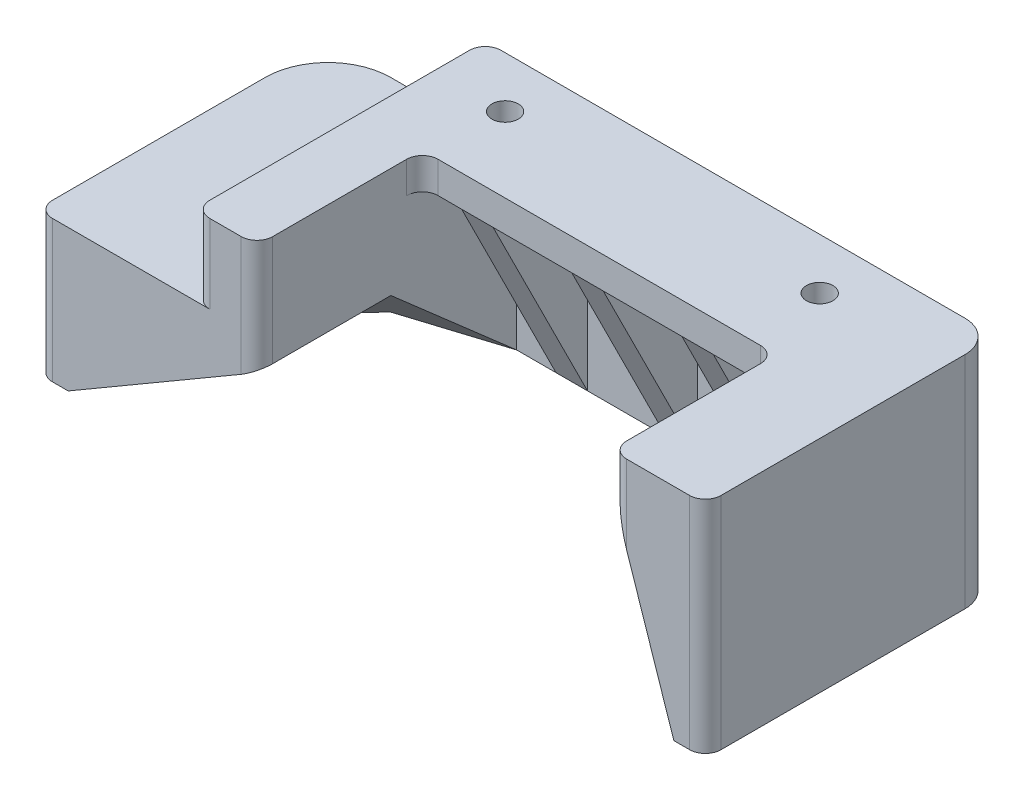
SolidWorks part; units mm, degrees
ref_plane "Front Plane" through (0, 0, 0) normal (0, 0, 1) x (1, 0, 0)
ref_plane "Top Plane" through (0, 0, 0) normal (0, 1, 0) x (1, 0, 0)
ref_plane "Right Plane" through (0, 0, 0) normal (1, 0, 0) x (0, 0, -1)
sketch "Sketch1" plane through (0, 0, 0) normal (0, 1, 0) x (-1, 0, 0)
  line L0 (0, 0) -> (141.2875, 0)
  line L2 (141.2875, 0) -> (141.2875, 65.1236)
  line L5 (0, 65.1236) -> (0, 0)
  line L6 (141.2875, 65.1236) -> (0, 65.1236)
  circle A0 centre (6.35, 16.6371) radius 2.667
  circle A9 centre (6.35, 42.0371) radius 2.667
  circle A10 centre (6.35, 67.4371) radius 2.667
  circle A11 centre (19.05, 16.6371) radius 2.667
  circle A12 centre (31.75, 16.6371) radius 2.667
  circle A13 centre (44.45, 16.6371) radius 2.667
  circle A14 centre (57.15, 16.6371) radius 2.667
  circle A15 centre (69.85, 16.6371) radius 2.667
  circle A16 centre (82.55, 16.6371) radius 2.667
  circle A17 centre (95.25, 16.6371) radius 2.667
  circle A18 centre (107.95, 16.6371) radius 2.667
  point P2 (0, 0)
  point P6 (0, 0)
  point P22 (0, 0)
  point P23 (0, 0)
  point P24 (0, 0)
  point P25 (-349.7027, -333.8065)
  point P28 (0, 0)
  point P29 (0, 0)
  point P30 (0, 0)
  point P31 (6.35, 42.0371)
  dimension "D1" = 5.334
  dimension "D4" = 25.4
  dimension "D5" = 25.4
  dimension "D6" = 9
  dimension "D7" = 12.7
  dimension "D2" = 65.1236
  dimension "D3" = 141.2875
  dimension "D8" = 6.35
  dimension "D9" = 16.6371
sketch "Sketch2" plane through (0, 0, 0) normal (0, 1, 0) x (1, 0, 0)
  line L0 (-141.2875, 0) -> (-141.2875, -65.1236) construction
  line L19 (-109.5375, -9.525) -> (-109.5375, -61.9486)
  line L20 (-6.35, -6.35) -> (-141.2875, -6.35)
  line L21 (-6.35, -65.1236) -> (-6.35, -6.35)
  line L22 (-12.7, -6.35) -> (-106.3625, -6.35)
  line L23 (-6.35, -61.9486) -> (-6.35, -12.7)
  line L27 (-106.3625, -65.1236) -> (-100.0125, -65.1236)
  line L28 (-141.2875, -65.1236) -> (0, -65.1236) construction
  line L29 (-96.8375, -61.9486) -> (-96.8375, -34.925)
  line L30 (-93.6625, -31.75) -> (-28.575, -31.75)
  line L31 (-25.4, -34.925) -> (-25.4, -61.9486)
  line L32 (-22.225, -65.1236) -> (-9.525, -65.1236)
  arc A4 (-6.35, -12.7) -> (-12.7, -6.35) centre (-12.7, -12.7) ccw
  circle A6 centre (-95.25, -16.6371) radius 2.667
  circle A7 centre (-31.75, -16.6371) radius 2.667
  arc A8 (-109.5375, -9.525) -> (-106.3625, -6.35) centre (-106.3625, -9.525) cw
  arc A12 (-100.0125, -65.1236) -> (-96.8375, -61.9486) centre (-100.0125, -61.9486) ccw
  arc A13 (-25.4, -61.9486) -> (-22.225, -65.1236) centre (-22.225, -61.9486) ccw
  arc A14 (-6.35, -61.9486) -> (-9.525, -65.1236) centre (-9.525, -61.9486) cw
  arc A15 (-28.575, -31.75) -> (-25.4, -34.925) centre (-28.575, -34.925) cw
  arc A16 (-96.8375, -34.925) -> (-93.6625, -31.75) centre (-93.6625, -34.925) cw
  arc A17 (-106.3625, -65.1236) -> (-109.5375, -61.9486) centre (-106.3625, -61.9486) cw
  point P3 (-115.8875, -65.1236)
  point P9 (0, 0)
  point P11 (-115.8875, -66.1497)
  point P23 (0, 0)
  point P26 (0, 0)
  point P30 (-109.5375, -6.35)
  point P31 (-109.5375, -65.1236)
  point P33 (-112.7125, -50.6865)
  point P34 (0, 0)
  point P42 (-96.8375, -65.1236)
  point P45 (-25.4, -65.1236)
  dimension "D1" = 6.35
  dimension "D2" = 6.35
  dimension "D3" = 19.05
  dimension "D7" = 25.4
  dimension "D4" = 5.334
  dimension "D9" = 3.175
  dimension "D10" = 3.175
  dimension "D5" = 31.75
  dimension "D8" = 12.7
extrude "Boss-Extrude1" add sketch "Sketch2" against normal blind 6.35
sketch "Sketch3" plane through (0, -6.35, 0) normal (0, -1, 0) x (1, 0, 0)
  line L0 (-6.35, 61.9486) -> (-6.35, 12.7) construction
  line L1 (-12.7, 6.35) -> (-106.3625, 6.35) construction
  line L2 (-6.35, 61.9486) -> (-6.35, 12.7)
  line L3 (-12.7, 6.35) -> (-96.8375, 6.35)
  line L4 (-96.8375, 6.35) -> (-96.8375, 12.7)
  line L5 (-12.7, 58.7736) -> (-12.7, 49.2486)
  line L6 (-15.875, 12.7) -> (-38.1, 12.7)
  line L7 (-12.7, 58.7736) -> (-12.7, 12.7) construction
  line L8 (-12.7, 12.7) -> (-96.8375, 12.7) construction
  line L9 (-6.35, 58.7736) -> (-6.35, 12.7) construction
  line L10 (-141.2875, 65.1236) -> (0, 65.1236) construction
  line L11 (-9.525, 65.1236) -> (-22.225, 65.1236)
  line L12 (-25.4, 61.9486) -> (-25.4, 58.7736)
  line L13 (-25.4, 34.925) -> (-25.4, 61.9486) construction
  line L14 (-25.4, 58.7736) -> (-12.7, 58.7736)
  line L15 (-12.7, 42.8986) -> (-25.4, 42.8986)
  line L16 (-25.4, 42.8986) -> (-25.4, 49.2486)
  line L17 (-25.4, 49.2486) -> (-12.7, 49.2486)
  line L18 (-12.7, 27.0236) -> (-25.4, 27.0236)
  line L19 (-25.4, 27.0236) -> (-25.4, 33.3736)
  line L20 (-25.4, 33.3736) -> (-12.7, 33.3736)
  line L21 (-12.7, 27.0236) -> (-12.7, 15.875)
  line L22 (-12.7, 42.8986) -> (-12.7, 33.3736)
  line L23 (-38.1, 12.7) -> (-38.1, 31.75)
  line L24 (-38.1, 31.75) -> (-44.45, 31.75)
  line L25 (-93.6625, 31.75) -> (-28.575, 31.75) construction
  line L26 (-44.45, 31.75) -> (-44.45, 12.7)
  line L27 (-44.45, 12.7) -> (-60.325, 12.7)
  line L28 (-60.325, 12.7) -> (-60.325, 31.75)
  line L29 (-60.325, 31.75) -> (-66.675, 31.75)
  line L30 (-66.675, 31.75) -> (-66.675, 12.7)
  line L31 (-88.9, 12.7) -> (-96.8375, 12.7)
  line L33 (-82.55, 12.7) -> (-82.55, 31.75)
  line L34 (-82.55, 31.75) -> (-88.9, 31.75)
  line L35 (-88.9, 12.7) -> (-88.9, 31.75)
  line L36 (-66.675, 12.7) -> (-82.55, 12.7)
  arc A0 (-12.7, 6.35) -> (-6.35, 12.7) centre (-12.7, 12.7) ccw construction
  arc A1 (-12.7, 6.35) -> (-6.35, 12.7) centre (-12.7, 12.7) ccw
  arc A2 (-22.225, 65.1236) -> (-25.4, 61.9486) centre (-22.225, 61.9486) ccw
  arc A4 (-6.35, 61.9486) -> (-9.525, 65.1236) centre (-9.525, 61.9486) ccw
  arc A5 (-12.7, 15.875) -> (-15.875, 12.7) centre (-15.875, 15.875) cw
  arc A6 (-12.7, 12.7) -> (-12.7, 12.7) centre (-12.7, 12.7) ccw construction
  point P33 (-25.4, 65.1236)
  point P36 (-6.35, 65.1236)
  dimension "D2" = 3.175
  dimension "D8" = 3.175
  dimension "D1" = 6.35
  dimension "D3" = 6.35
  dimension "D4" = 6.35
  dimension "D5" = 9.525
  dimension "D6" = 6.35
  dimension "D7" = 9.525
  dimension "D9" = 6.35
  dimension "D10" = 6.35
  dimension "D11" = 6.35
  dimension "D12" = 6.35
  dimension "D13" = 15.875
  dimension "D14" = 15.875
extrude "Boss-Extrude2" add sketch "Sketch3" along normal blind 38.1
sketch "Sketch4" plane through (-88.9, 0, 0) normal (-1, 0, 0) x (0, 0, 1)
  line L0 (31.75, -6.35) -> (12.7, -44.45)
  line L1 (31.75, -44.45) -> (12.7, -44.45) construction
  line L2 (12.7, -44.45) -> (12.7, -6.35) construction
  line L3 (12.7, -44.45) -> (31.75, -44.45)
  line L4 (31.75, -44.45) -> (31.75, -6.35)
extrude "Cut-Extrude1" cut sketch "Sketch4" against normal up to surface (50.8 mm away) up to face at (-38.1, -25.4, 22.225)
sketch "Sketch5" plane through (0, 0, 65.1236) normal (0, 0, 1) x (1, 0, 0)
  line L0 (-25.4, -6.35) -> (-12.7, -44.45)
  line L1 (-9.525, -44.45) -> (-22.225, -44.45) construction
  line L2 (-12.7, -44.45) -> (-25.4, -44.45)
  line L3 (-25.4, -44.45) -> (-25.4, -6.35)
  point P5 (0, 0)
extrude "Cut-Extrude2" cut sketch "Sketch5" against normal up to surface (38.1 mm away) up to face at (-19.05, -25.4, 27.0236)
sketch "Sketch6" plane through (0, -6.35, 0) normal (0, -1, 0) x (1, 0, 0)
  line L0 (-96.8375, 6.35) -> (-106.3625, 6.35) construction
  line L1 (-109.5375, 9.525) -> (-109.5375, 61.9486) construction
  line L2 (-96.8375, 6.35) -> (-106.3625, 6.35)
  line L3 (-109.5375, 9.525) -> (-109.5375, 61.9486)
  line L4 (-106.3625, 65.1236) -> (-100.0125, 65.1236)
  line L5 (-96.8375, 61.9486) -> (-96.8375, 6.35)
  arc A0 (-109.5375, 9.525) -> (-106.3625, 6.35) centre (-106.3625, 9.525) ccw construction
  arc A1 (-106.3625, 65.1236) -> (-109.5375, 61.9486) centre (-106.3625, 61.9486) ccw construction
  arc A2 (-96.8375, 61.9486) -> (-100.0125, 65.1236) centre (-100.0125, 61.9486) ccw construction
  arc A3 (-109.5375, 9.525) -> (-106.3625, 6.35) centre (-106.3625, 9.525) ccw
  arc A4 (-106.3625, 65.1236) -> (-109.5375, 61.9486) centre (-106.3625, 61.9486) ccw
  arc A5 (-96.8375, 61.9486) -> (-100.0125, 65.1236) centre (-100.0125, 61.9486) ccw
extrude "Boss-Extrude3" add sketch "Sketch6" along normal blind 9.525
sketch "Sketch7" plane through (0, -15.875, 0) normal (0, -1, 0) x (1, 0, 0)
  line L0 (-100.0125, 65.1236) -> (-138.1125, 65.1236)
  line L1 (-141.2875, 61.9486) -> (-141.2875, 19.05)
  line L2 (-141.2875, 0) -> (-141.2875, 65.1236) construction
  line L3 (-128.5875, 6.35) -> (-96.8375, 6.35)
  line L4 (-96.8375, 6.35) -> (-96.8375, 61.9486)
  arc A0 (-96.8375, 61.9486) -> (-100.0125, 65.1236) centre (-100.0125, 61.9486) ccw construction
  arc A1 (-96.8375, 61.9486) -> (-100.0125, 65.1236) centre (-100.0125, 61.9486) ccw
  arc A2 (-138.1125, 65.1236) -> (-141.2875, 61.9486) centre (-138.1125, 61.9486) ccw
  arc A3 (-141.2875, 19.05) -> (-128.5875, 6.35) centre (-128.5875, 19.05) ccw
  point P12 (-141.2875, 65.1236)
  point P15 (-141.2875, 6.35)
  dimension "D1" = 3.175
  dimension "D2" = 12.7
extrude "Boss-Extrude4" add sketch "Sketch7" along normal blind 6.35
sketch "Sketch8" plane through (0, -22.225, 0) normal (0, -1, 0) x (1, 0, 0)
  line L0 (-128.5875, 6.35) -> (-96.8375, 6.35) construction
  line L1 (-128.5875, 6.35) -> (-96.8375, 6.35)
  line L2 (-141.2875, 61.9486) -> (-141.2875, 19.05)
  line L3 (-134.9375, 58.7736) -> (-134.9375, 52.4236)
  line L4 (-128.5875, 12.7) -> (-103.1875, 12.7)
  line L5 (-134.9375, 61.9486) -> (-134.9375, 19.05) construction
  line L6 (-82.55, 31.75) -> (-66.675, 31.75) construction
  line L8 (-96.8375, 12.7) -> (-96.8375, 6.35)
  line L9 (-96.8375, 12.7) -> (-96.8375, 14.494) construction
  line L10 (-138.1125, 65.1236) -> (-100.0125, 65.1236)
  line L12 (-134.9375, 58.7736) -> (-96.8375, 58.7736)
  line L13 (-96.8375, 61.9486) -> (-96.8375, 58.7736)
  line L14 (-134.9375, 52.4236) -> (-96.8375, 52.4236)
  line L16 (-134.9375, 46.0736) -> (-96.8375, 46.0736)
  line L17 (-96.8375, 52.4236) -> (-96.8375, 46.0736)
  line L18 (-134.9375, 38.1) -> (-96.8375, 38.1)
  line L20 (-134.9375, 31.75) -> (-103.1875, 31.75)
  line L27 (-103.1875, 12.7) -> (-103.1875, 31.75)
  line L29 (-96.8375, 12.7) -> (-96.8375, 38.1)
  line L30 (-134.9375, 31.75) -> (-134.9375, 19.05)
  line L31 (-134.9375, 46.0736) -> (-134.9375, 38.1)
  line L32 (-128.5875, 12.7) -> (-96.8375, 12.7) construction
  line L34 (-96.8375, 12.7) -> (-96.8375, 61.9486) construction
  arc A0 (-141.2875, 19.05) -> (-128.5875, 6.35) centre (-128.5875, 19.05) ccw construction
  arc A1 (-138.1125, 65.1236) -> (-141.2875, 61.9486) centre (-138.1125, 61.9486) ccw construction
  arc A2 (-141.2875, 19.05) -> (-128.5875, 6.35) centre (-128.5875, 19.05) ccw
  arc A3 (-138.1125, 65.1236) -> (-141.2875, 61.9486) centre (-138.1125, 61.9486) ccw
  arc A4 (-134.9375, 19.05) -> (-128.5875, 12.7) centre (-128.5875, 19.05) ccw
  arc A5 (-100.0125, 65.1236) -> (-96.8375, 61.9486) centre (-100.0125, 61.9486) cw
  point P15 (-96.8375, 65.1236)
  point P26 (0, 0)
  point P27 (0, 0)
  point P28 (-103.1875, 29.3259)
  point P31 (-103.1875, 38.9691)
  point P36 (0, 0)
  point P37 (-139.0727, 65.1236)
  dimension "D5" = 3.175
  dimension "D1" = 6.35
  dimension "D2" = 6.35
  dimension "D3" = 6.35
  dimension "D4" = 6.35
  dimension "D6" = 6.35
  dimension "D7" = 6.35
extrude "Boss-Extrude5" add sketch "Sketch8" along normal up to surface (22.225 mm away) up to face at (-35.5872, -44.45, 27.2537)
sketch "Sketch11" plane through (0, 0, 65.1236) normal (0, 0, 1) x (1, 0, 0)
  line L0 (-134.9375, -44.45) -> (-96.8375, -22.225)
  line L1 (-100.0125, -44.45) -> (-138.1125, -44.45) construction
  line L2 (-96.8375, -22.225) -> (-96.8375, -44.45)
  line L3 (-96.8375, -44.45) -> (-134.9375, -44.45)
  line L4 (-96.8375, -44.45) -> (-96.8375, 0) construction
  point P7 (0, 0)
  point P9 (0, 0)
extrude "Cut-Extrude4" cut sketch "Sketch11" against normal up to surface (19.05 mm away) up to face at (-115.8875, -33.3375, 46.0736)
ref_plane "Plane1" through (-0.2565, 0.4397, -0.3848) normal (-0.402, 0.6891, -0.603) x (0.9157, 0.3025, -0.2647)
sketch "Sketch23" plane through (-0.2565, 0.4397, -0.3848) normal (-0.402, 0.6891, -0.603) x (0.9157, 0.3025, -0.2647)
  line L0 (-105.4779, 19.7128) -> (-105.4779, -14.0379)
  line L1 (-105.4779, -14.0379) -> (-147.0877, 0.5974)
  line L2 (-147.0877, 0.5974) -> (-105.4779, 19.7128)
extrude "Cut-Extrude7" cut sketch "Sketch23" against normal blind 19.05
sketch "Sketch24" plane through (-103.1875, 0, 0) normal (-1, 0, 0) x (0, 0, 1)
  line L0 (31.75, -31.4854) -> (12.7, -44.45)
  line L1 (12.7, -44.45) -> (16.9333, -44.45)
  line L2 (16.9333, -44.45) -> (31.75, -31.4854)
extrude "Cut-Extrude8" cut sketch "Sketch24" against normal up to surface (6.35 mm away) up to face at (-96.8375, -15.0812, 37.316)
sketch "Sketch25" plane through (0, 0, 31.75) normal (0, 0, -1) x (-1, 0, 0)
  line L0 (103.1875, -31.4854) -> (134.9375, -44.45)
  line L1 (134.9375, -44.45) -> (125.4125, -44.45)
  line L2 (125.4125, -44.45) -> (134.9375, -44.45) construction
  line L3 (103.1875, -31.4854) -> (125.4125, -44.45) construction
  line L4 (125.4125, -44.45) -> (103.1875, -31.4854)
extrude "Cut-Extrude9" cut sketch "Sketch25" against normal up to surface (6.35 mm away) up to face at (-122.2375, -29.6333, 38.1)
equation "\"D3\"=1.58333"
